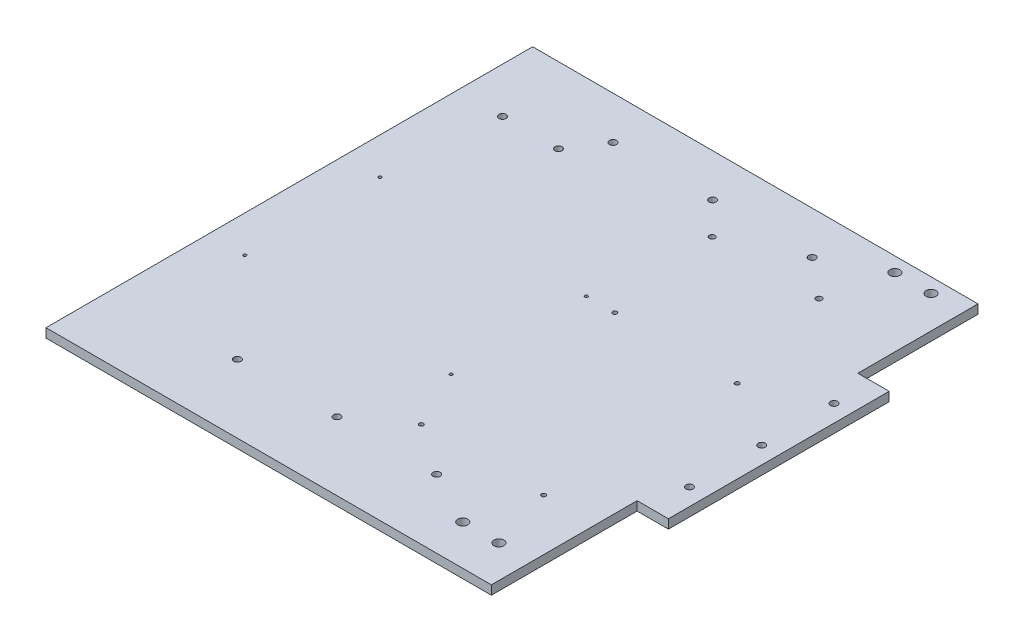
SolidWorks part; units mm, degrees
material "Cedar"
ref_plane "Front Plane" through (0, 0, 0) normal (0, 0, 1) x (1, 0, 0)
ref_plane "Top Plane" through (0, 0, 0) normal (0, 1, 0) x (1, 0, 0)
ref_plane "Right Plane" through (0, 0, 0) normal (1, 0, 0) x (0, 0, -1)
sketch "Sketch1" plane through (0, 0, 0) normal (0, 1, 0) x (1, 0, 0)
  line L0 (72.8376, -16.2766) -> (72.8376, -52.4668) construction
  line L1 (-156.5, -171) -> (156.5, -171)
  line L2 (-156.5, -171) -> (-156.5, 171)
  line L3 (-156.5, 171) -> (156.5, 171)
  line L4 (156.5, -171) -> (156.5, 171)
  line L5 (-156.5, -171) -> (156.5, 171) construction
  line L6 (-156.5, 171) -> (156.5, -171) construction
  point P0 (0, 0)
  dimension "D1" = 342
  dimension "D2" = 313
extrude "Boss-Extrude1" add sketch "Sketch1" against normal blind 6.35
ref_plane "Plane1" through (0, 0, -9) normal (0, 0, -1) x (-1, 0, 0)
sketch "Sketch3" plane through (0, 0, 0) normal (0, 1, 0) x (1, 0, 0)
  line L0 (156.5, 9) -> (-156.5, 9) construction
  line L1 (156.5, -171) -> (156.5, 171) construction
  line L2 (-156.5, 171) -> (-156.5, -171) construction
  line L3 (55, 9) -> (-55, 9) construction
  line L4 (156.5, 86.5702) -> (156.5, -68.5702)
  line L5 (156.5, -68.5702) -> (178.5, -68.5702)
  line L6 (178.5, -68.5702) -> (178.5, 86.5702)
  line L7 (178.5, 86.5702) -> (156.5, 86.5702)
  line L8 (166.5, 59.8) -> (166.5, 9) construction
  circle A0 centre (166.5, 9) radius 2.5
  circle A1 centre (166.5, -41.8) radius 2.5
  circle A2 centre (166.5, 59.8) radius 2.5
  point P10 (156.5, 9)
  dimension "D2" = 5
  dimension "D4" = 5
  dimension "D5" = 50.8
  dimension "D1" = 22
  dimension "D3" = 10
  dimension "D6" = 0
  dimension "D7" = 155.1404
extrude "Boss-Extrude2" add sketch "Sketch3" against normal blind 6.35
sketch "Sketch2" plane through (0, 0, 0) normal (0, 1, 0) x (1, 0, 0)
  line L0 (156.5, 9) -> (-156.5, 9) construction
  line L1 (156.5, -171) -> (156.5, -68.5702) construction
  line L2 (-156.5, 171) -> (-156.5, -171) construction
  line L3 (0, -123) -> (0, -171) construction
  line L4 (55, 9) -> (-55, 9) construction
  line L5 (156.5, -123) -> (-156.5, -123) construction
  line L6 (-156.5, -171) -> (156.5, -171) construction
  circle A0 centre (0, -123) radius 2.5
  circle A1 centre (-70, -123) radius 2.5
  circle A2 centre (70, -123) radius 2.5
  circle A3 centre (-70, 141) radius 2.5
  circle A4 centre (0, 141) radius 2.5
  circle A5 centre (70, 141) radius 2.5
  dimension "D2" = 5
  dimension "D3" = 5
  dimension "D4" = 70
  dimension "D1" = 132
extrude "Cut-Extrude1" cut sketch "Sketch2" against normal through all
sketch "Sketch4" plane through (0, 0, 0) normal (0, 1, 0) x (1, 0, 0)
  line L0 (156.5, -171) -> (156.5, -68.5702) construction
  line L1 (108.24, -142.84) -> (133.64, -142.84) construction
  line L2 (-156.5, -171) -> (156.5, -171) construction
  circle A0 centre (133.64, -142.84) radius 3.5
  circle A1 centre (108.24, -142.84) radius 3.5
  dimension "D1" = 7
  dimension "D2" = 7
  dimension "D3" = 25.4
  dimension "D4" = 22.86
  dimension "D5" = 28.16
extrude "Cut-Extrude2" cut sketch "Sketch4" against normal through all
mirror "Mirror1" about plane through (0, 0, -9) normal (0, 0, -1) of "Cut-Extrude2"
sketch "Sketch5" plane through (0, 0, 0) normal (0, 1, 0) x (1, 0, 0)
  circle A27 centre (97.3856, 118.3655) radius 2
  circle A28 centre (22.3343, 118.3655) radius 2
  circle A29 centre (120.259, -98.0187) radius 1.5
  circle A30 centre (34.259, -98.0187) radius 1.5
  circle A31 centre (34.259, 37.9813) radius 1.5
  circle A32 centre (120.259, 37.9813) radius 1.5
  circle A33 centre (14.259, -57.0187) radius 1.05
  circle A34 centre (-130.741, -57.0187) radius 1.05
  circle A35 centre (14.259, 37.9813) radius 1.05
  circle A36 centre (-130.741, 37.9813) radius 1.05
  circle A37 centre (-85.3157, 117.9803) radius 2.5
  circle A38 centre (-124.6657, 117.9803) radius 2.5
extrude "Cut-Extrude3" cut sketch "Sketch5" against normal through all
